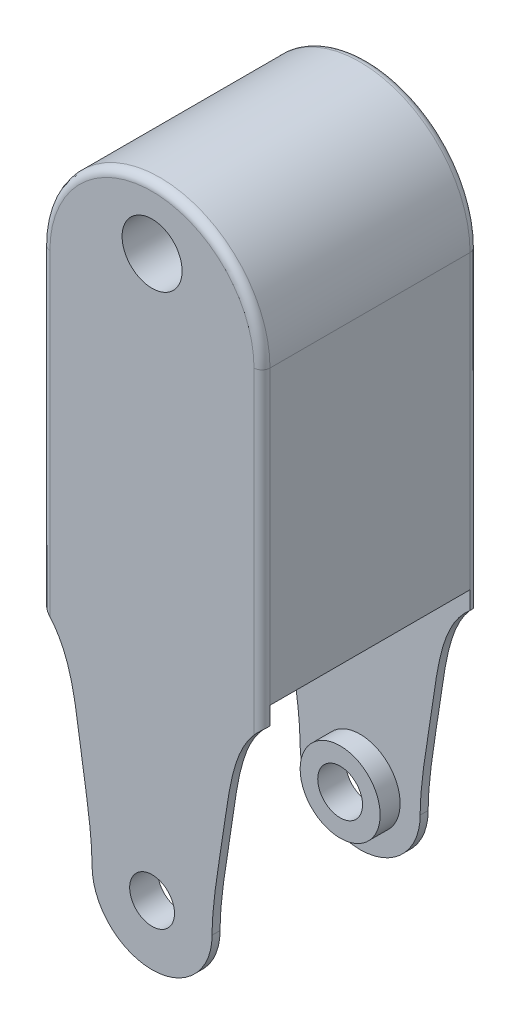
SolidWorks part; units mm, degrees
ref_plane "Alzado" through (0, 0, 0) normal (0, 0, 1) x (1, 0, 0)
ref_plane "Planta" through (0, 0, 0) normal (0, 1, 0) x (1, 0, 0)
ref_plane "Vista lateral" through (0, 0, 0) normal (1, 0, 0) x (0, 0, -1)
sketch "Croquis1" plane through (0, 0, 0) normal (0, 0, 1) x (1, 0, 0)
  line L2 (74, 180) -> (37, 180) construction
  line L3 (0, 143) -> (0, 70)
  line L4 (74, 143) -> (74, 180) construction
  line L6 (37, 0) -> (37, 15)
  line L7 (37, 15) -> (37, 40) construction
  line L8 (37, 40) -> (19, 40) construction
  line L9 (74, 143) -> (74, 70)
  line L10 (74, 70) -> (74, 0) construction
  line L11 (37, 180) -> (37, 155) construction
  arc A0 (74, 143) -> (0, 143) centre (37, 143) ccw
  circle A2 centre (37, 15) radius 5.6
  arc A3 (22, 15) -> (52, 15) centre (37, 15) ccw
  circle A4 centre (37, 155) radius 7.5
  spline S0 degree 3 poles (52, 15) (52, 22.318) (56.2223, 44.5245) (58.0965, 66.3006) (74, 70) knots 0 0 0 0 0.399675 1 1 1 1
  spline S1 degree 3 poles (22, 15) (22, 22.318) (17.7777, 44.5245) (15.9035, 66.3006) (0, 70) knots 0 0 0 0 0.399675 1 1 1 1
  dimension "D3" = 15
  dimension "D4" = 11.2
  dimension "D9" = 15
  dimension "D1" = 180
  dimension "D2" = 74
  dimension "D5" = 15
  dimension "D6" = 25
  dimension "D7" = 18
  dimension "D8" = 20
  dimension "D11" = 25
extrude "Saliente-Extruir1" add sketch "Croquis1" along normal blind 54
sketch "Croquis2" plane through (74, 0, 0) normal (1, 0, 0) x (0, 0, -1)
  line L0 (-54, 70) -> (-52, 70) construction
  line L1 (-54, 70) -> (0, 70) construction
  line L2 (-52, 70) -> (-2, 70)
  line L3 (-2, 70) -> (0, 70) construction
  line L4 (-52, 70) -> (-52, 20.6)
  line L9 (-52, 20.6) -> (-49, 20.6)
  line L10 (-49, 20.6) -> (-49, 9.4)
  line L11 (-52, 9.4) -> (-49, 9.4)
  line L12 (-52, 9.4) -> (-52, 0)
  line L17 (-2, 9.4) -> (-2, 0)
  line L18 (-2, 9.4) -> (-5, 9.4)
  line L19 (-5, 20.6) -> (-5, 9.4)
  line L20 (-2, 20.6) -> (-5, 20.6)
  line L21 (-2, 70) -> (-2, 20.6)
  line L22 (0, 70) -> (-2, 70) construction
  line L27 (-52, 0) -> (-2, 0)
  point P16 (-49, 15)
  point P31 (-5, 15)
  point P32 (-50.5, 9.4)
  dimension "D1" = 11.2
  dimension "D4" = 3
sketch "Croquis6" plane through (0, 0, 0) normal (-1, 0, 0) x (0, 0, 1)
  line L0 (0, 70) -> (0, 0)
  line L1 (0, 0) -> (54, 0)
  line L2 (54, 0) -> (54, 70)
  line L3 (54, 70) -> (0, 70)
extrude "Saliente-Extruir3" add sketch "Croquis6" against normal blind 74
sketch "Croquis7" plane through (74, 0, 0) normal (1, 0, 0) x (0, 0, -1)
  line L0 (-52, 0) -> (-2, 0)
  line L1 (-2, 0) -> (-2, 9.4)
  line L2 (-2, 9.4) -> (-5, 9.4)
  line L3 (-5, 9.4) -> (-5, 20.6)
  line L4 (-5, 20.6) -> (-2, 20.6)
  line L5 (-2, 20.6) -> (-2, 70)
  line L6 (-2, 70) -> (-52, 70)
  line L7 (-52, 70) -> (-52, 20.6)
  line L8 (-52, 20.6) -> (-49, 20.6)
  line L9 (-49, 20.6) -> (-49, 9.4)
  line L10 (-49, 9.4) -> (-52, 9.4)
  line L11 (-52, 9.4) -> (-52, 0)
extrude "Cortar-Extruir13" cut sketch "Croquis7" against normal blind 74
sketch "Croquis8" plane through (0, 0, 0) normal (0, 0, -1) x (-1, 0, 0)
  line L0 (-74, 70) -> (-74, 0)
  line L1 (-74, 0) -> (-37, 0)
  line L2 (-37, 0) -> (0, 0)
  line L3 (0, 0) -> (0, 70)
  circle A0 centre (-37, 15) radius 5.6
  arc A1 (-52, 15) -> (-22, 15) centre (-37, 15) ccw
  spline S0 degree 3 poles (-74, 70) (-58.0965, 66.3006) (-56.2223, 44.5245) (-52, 22.318) (-52, 15) knots 0 0 0 0 0.600325 1 1 1 1
  spline S1 degree 3 poles (-22, 15) (-22, 22.318) (-17.7777, 44.5245) (-15.9035, 66.3006) (0, 70) knots 0 0 0 0 0.399675 1 1 1 1
  line M1 (-74, 0) -> (0, 0)
  line M2 (0, 0) -> (0, 143)
  line M4 (-74, 143) -> (-74, 0)
extrude "Cortar-Extruir14" cut sketch "Croquis8" against normal blind 74 contours S0 A1 M4 M1 | S1 A1 M1 M2
sketch "Croquis9" plane through (74, 0, 0) normal (1, 0, 0) x (0, 0, -1)
  line L0 (-49, 20.6) -> (-52, 20.6)
  line L1 (-52, 20.6) -> (-52, 9.4)
  line L2 (-52, 9.4) -> (-49, 9.4)
  line L3 (-49, 9.4) -> (-49, 20.6)
  line L4 (-2, 20.6) -> (-5.1988, 20.6)
  line L5 (-5.1988, 20.6) -> (-5, 9.4)
  line L6 (-5, 9.4) -> (-2, 9.4)
  line L7 (-2, 20.6) -> (-2, 9.4)
extrude "Cortar-Extruir15" cut sketch "Croquis9" against normal blind 74
sketch "Croquis10" plane through (0, 0, 0) normal (0, 0, -1) x (-1, 0, 0)
  circle A0 centre (-37, 15) radius 5.6
extrude "Cortar-Extruir16" cut sketch "Croquis10" against normal blind 74
sketch "Croquis11" plane through (0, 0, 52) normal (0, 0, -1) x (-1, 0, 0)
  circle A0 centre (-37, 15) radius 10
  circle A1 centre (-37, 15) radius 5.6
  dimension "D1" = 20
extrude "Saliente-Extruir4" add sketch "Croquis11" along normal blind 5
sketch "Croquis12" plane through (0, 0, 2) normal (0, 0, 1) x (1, 0, 0)
  circle A0 centre (37, 15) radius 5.6
  circle A1 centre (37, 15) radius 10
  dimension "D1" = 20
extrude "Saliente-Extruir5" add sketch "Croquis12" along normal blind 5
sketch "Croquis13" plane through (0, 0, 0) normal (-1, 0, 0) x (0, 0, 1)
  line L0 (2, 70) -> (2, 143)
  line L1 (54, 143) -> (0, 143) construction
  line L2 (2, 143) -> (52, 143)
  line L3 (52, 143) -> (52, 70)
  line L4 (52, 70) -> (2, 70)
extrude "Cortar-Extruir17" cut sketch "Croquis13" against normal blind 74
sketch "Croquis14" plane through (0, 0, 0) normal (0, 0, -1) x (-1, 0, 0)
  line L0 (-74, 70) -> (0, 70)
  line L1 (0, 143) -> (0, 70) construction
  line L2 (-74, 143) -> (0, 143)
  line L3 (0, 70) -> (0, 143)
  line L4 (-74, 143) -> (-74, 70)
extrude "Saliente-Extruir6" add sketch "Croquis14" against normal blind 54
sketch "Croquis15" plane through (0, 0, 54) normal (0, 0, 1) x (1, 0, 0)
  line L0 (9.4707, 142.9909) -> (9.4707, 62.1377)
  line L1 (9.4707, 62.1377) -> (-11.5189, 62.1377)
  line L2 (-11.5189, 62.1377) -> (-11.5189, 188.6924)
  line L3 (-11.5189, 188.6924) -> (98.8649, 188.6924)
  line L4 (98.8649, 188.6924) -> (98.8649, 62.1377)
  line L5 (64.4707, 142.9909) -> (64.4707, 62.1377)
  line L6 (64.4707, 62.1377) -> (98.8649, 62.1377)
  arc A1 (64.4707, 142.9909) -> (9.4707, 142.9909) centre (36.9707, 142.9909) ccw
  dimension "D1" = 55
extrude "Cortar-Extruir18" cut sketch "Croquis15" against normal blind 54
fillet "Redondeo3" radius 2 6 edges at (9.4707, 65.5542, 53) (64.4707, 65.5053, 53) (9.4707, 104.2725, 54) (36.9707, 170.4909, 54) (64.4707, 104.2481, 54)
fillet "Redondeo4" radius 2 6 edges at (9.4707, 65.5542, 1) (64.4707, 65.5053, 1) (36.9707, 170.4909, 0) (9.4707, 104.2725, 0) (64.4707, 104.2481, 0)
